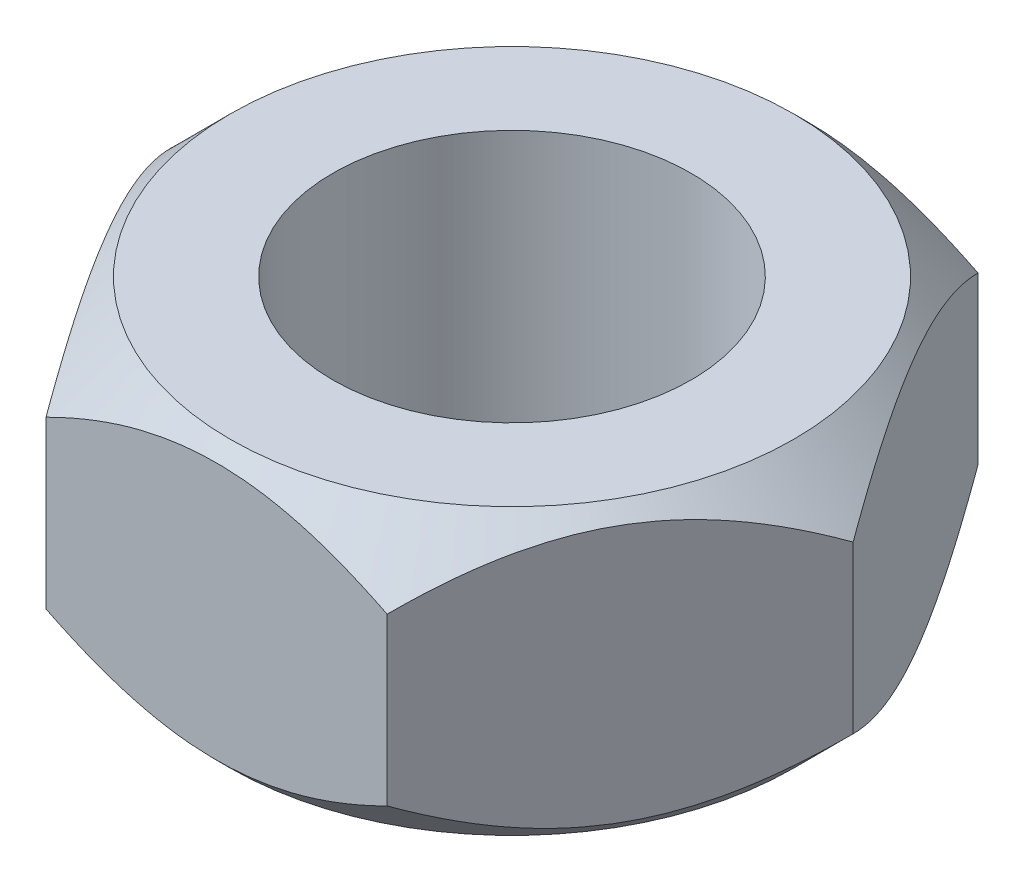
SolidWorks part; units mm, degrees
ref_plane "Front Plane" through (0, 0, 0) normal (0, 0, 1) x (1, 0, 0)
ref_plane "Top Plane" through (0, 0, 0) normal (0, 1, 0) x (1, 0, 0)
ref_plane "Right Plane" through (0, 0, 0) normal (1, 0, 0) x (0, 0, -1)
sketch "Sketch1" plane through (0, 0, 0) normal (0, 1, 0) x (1, 0, 0)
  line L1 (-7.188, 0) -> (-3.594, -6.225)
  line L2 (-3.594, -6.225) -> (3.594, -6.225)
  line L3 (3.594, -6.225) -> (7.188, 0)
  line L4 (7.188, 0) -> (3.594, 6.225)
  line L5 (3.594, 6.225) -> (-3.594, 6.225)
  line L6 (-3.594, 6.225) -> (-7.188, 0)
  circle A0 centre (0, 0) radius 6.225 construction
  circle A1 centre (0, 0) radius 3.775
  point P1 (0, -6.225)
  dimension "D2" = 7.55
  dimension "D1" = 12.45
extrude "Boss-Extrude1" add sketch "Sketch1" along normal blind 6
ref_plane "Plane1" through (0, 0, 0) normal (0, 0, 1) x (1, 0, 0)
sketch "Sketch5" plane through (0, 0, 0) normal (0, 0, 1) x (1, 0, 0)
  line L0 (0, 0) -> (0, 7.3063) construction
  line L1 (-3.594, 0) -> (3.594, 0) construction
  line L7 (-5.938, 6) -> (-7.188, 6)
  line L8 (-7.188, 6) -> (-3.594, 6) construction
  line L9 (-7.188, 6) -> (-7.188, 4.75)
  line L10 (-7.188, 6) -> (-7.188, 0) construction
  line L11 (-7.188, 4.75) -> (-5.938, 6)
  line L12 (-7.188, 3) -> (-2.2678, 3) construction
  line L13 (-5.938, 0) -> (-7.188, 0)
  line L14 (-7.188, 0) -> (-7.188, 1.25)
  line L15 (-7.188, 1.25) -> (-5.938, 0)
  dimension "D1" = 1.25
  dimension "D2" = 1.25
revolve "Cut-Revolve1" cut sketch "Sketch5" angle 360 about L0
